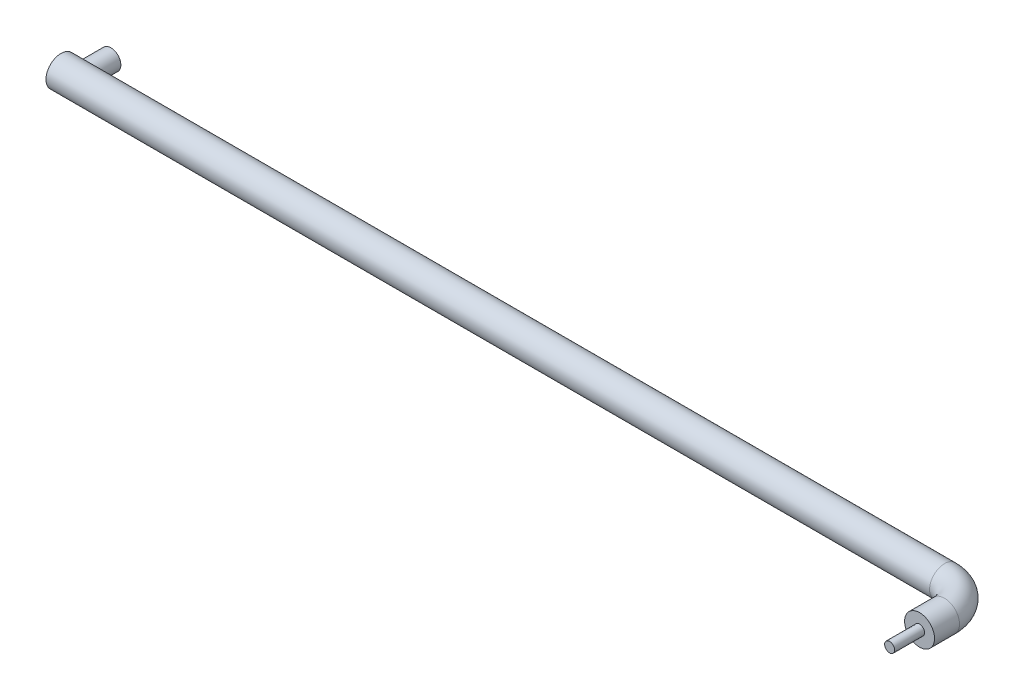
SolidWorks part; units mm, degrees
ref_plane "Front Plane" through (0, 0, 0) normal (0, 0, 1) x (1, 0, 0)
ref_plane "Top Plane" through (0, 0, 0) normal (0, 1, 0) x (1, 0, 0)
ref_plane "Right Plane" through (0, 0, 0) normal (1, 0, 0) x (0, 0, -1)
sketch "Sketch1" plane through (0, 0, 0) normal (0, 1, 0) x (1, 0, 0)
  line L0 (0, 0) -> (885, 0)
  line L1 (915, -30) -> (915, -55)
  arc A0 (885, 0) -> (915, -30) centre (885, -30) cw
  point P6 (915, 0)
  dimension "D3" = 30
  dimension "D1" = 915
  dimension "D2" = 55
sketch "Sketch2" plane through (0, 0, 0) normal (1, 0, 0) x (0, 0, -1)
  circle A0 centre (0, 0) radius 15
sweep "Sweep2" add profiles "Sketch2" path "Sketch1"
sketch "Sketch3" plane through (0, 0, 55) normal (0, 0, 1) x (1, 0, 0)
  circle A0 centre (915, 0) radius 5
extrude "Boss-Extrude1" add sketch "Sketch3" along normal blind 30
sketch "Sketch4" plane through (0, 0, 0) normal (0, 0, 1) x (1, 0, 0)
  line L0 (0, 0) -> (15, 0) construction
  circle A0 centre (15, 0) radius 10
  dimension "D1" = 15
extrude "Boss-Extrude2" add sketch "Sketch4" against normal blind 35
sketch "Sketch5" plane through (0, 0, 0) normal (0, 1, 0) x (1, 0, 0)
  line L0 (0, -11.618) -> (0, 48.5663) construction
  line L1 (0, 15) -> (0, -15) construction
  line L2 (930, -55) -> (930, 55.6271) construction
  line L3 (930, 55.6271) -> (0, 55.6271) construction
  dimension "D1" = 930
